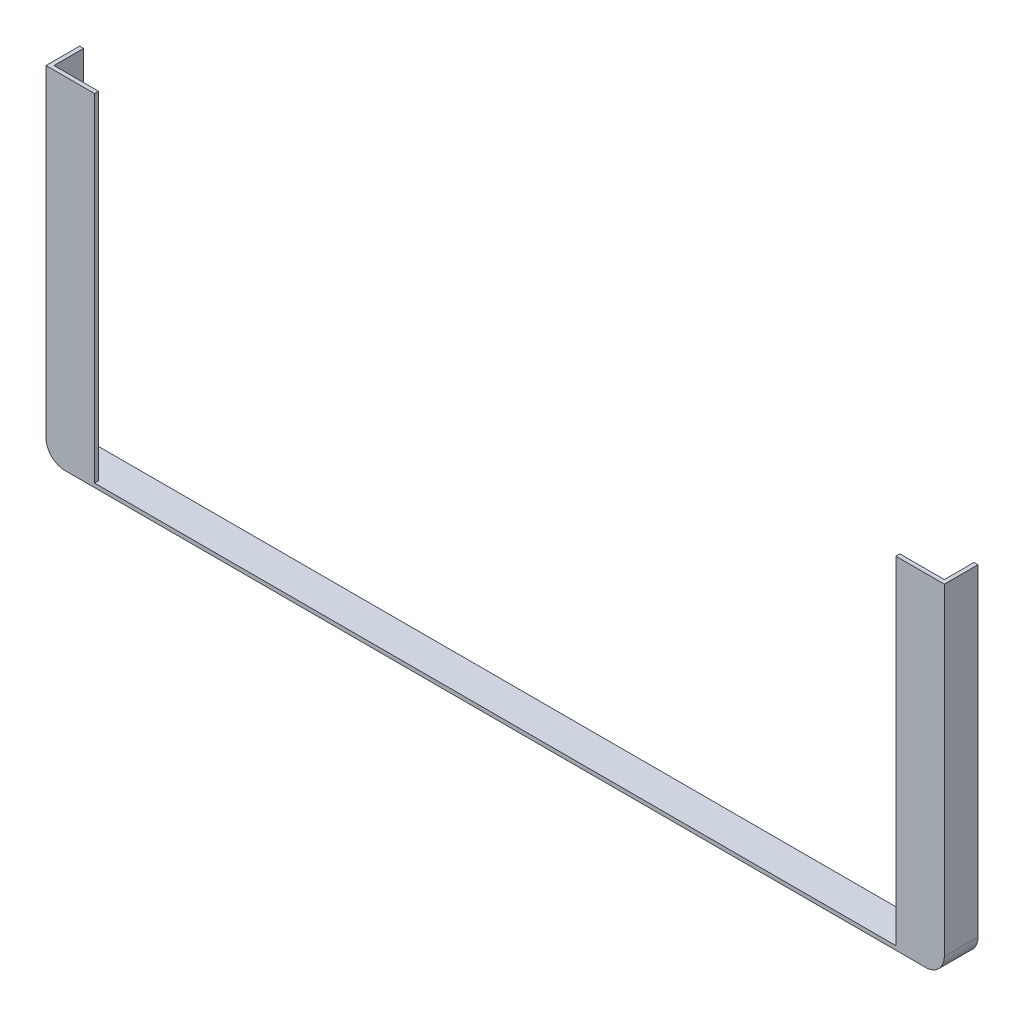
SolidWorks part; units mm, degrees
material "Plain Carbon Steel"
ref_plane "Front Plane" through (0, 0, 0) normal (0, 0, 1) x (1, 0, 0)
ref_plane "Top Plane" through (0, 0, 0) normal (0, 1, 0) x (1, 0, 0)
ref_plane "Right Plane" through (0, 0, 0) normal (1, 0, 0) x (0, 0, -1)
sketch "Sketch2" plane through (0, 0, 0) normal (0, 0, 1) x (1, 0, 0)
  line L1 (-381, 12.7) -> (-381, 288.6837)
  line L4 (381, 12.7) -> (381, 288.6837)
  line L5 (-368.3, 0) -> (368.3, 0)
  line L6 (384.4163, 12.7) -> (384.4163, 288.6837)
  line L7 (-368.3, -3.4163) -> (368.3, -3.4163)
  line L8 (-384.4163, 12.7) -> (-384.4163, 288.6837)
  line L9 (381, 288.6837) -> (384.4163, 288.6837)
  line L10 (-384.4163, 288.6837) -> (-381, 288.6837)
  arc A2 (368.3, 0) -> (381, 12.7) centre (368.3, 12.7) ccw
  arc A3 (-381, 12.7) -> (-368.3, 0) centre (-368.3, 12.7) ccw
  arc A4 (368.3, -3.4163) -> (384.4163, 12.7) centre (368.3, 12.7) ccw
  arc A5 (-384.4163, 12.7) -> (-368.3, -3.4163) centre (-368.3, 12.7) ccw
  point P16 (0, 0)
  dimension "D2" = 12.7
  dimension "D3" = 292.1
  dimension "D4" = 768.8326
  dimension "D1" = 3.4163
extrude "Side" add sketch "Sketch2" against normal blind 25.4
sketch "Sketch3" plane through (0, 0, 0) normal (0, 0, 1) x (1, 0, 0)
  line L0 (-368.3, -3.4163) -> (368.3, -3.4163) construction
  line L1 (-384.4163, 288.6837) -> (-384.4163, 12.7) construction
  line L2 (-368.3, -3.4163) -> (368.3, -3.4163)
  line L3 (-384.4163, 288.6837) -> (-384.4163, 12.7)
  line L4 (384.4163, 12.7) -> (384.4163, 288.6837) construction
  line L5 (384.4163, 12.7) -> (384.4163, 288.6837)
  line L6 (384.4163, 288.6837) -> (-384.4163, 288.6837)
  arc A0 (-384.4163, 12.7) -> (-368.3, -3.4163) centre (-368.3, 12.7) ccw construction
  arc A1 (-384.4163, 12.7) -> (-368.3, -3.4163) centre (-368.3, 12.7) ccw
  arc A2 (368.3, -3.4163) -> (384.4163, 12.7) centre (368.3, 12.7) ccw construction
  arc A3 (368.3, -3.4163) -> (384.4163, 12.7) centre (368.3, 12.7) ccw
extrude "Panel" add sketch "Sketch3" along normal blind 3.4163
sketch "Sketch4" plane through (0, 0, 0) normal (0, 0, -1) x (-1, 0, 0)
  line L0 (-368.3, 0) -> (368.3, 0) construction
  line L1 (-342.9, 0) -> (342.9, 0)
  line L2 (-342.9, 0) -> (-342.9, 288.6837)
  line L3 (-342.9, 288.6837) -> (342.9, 288.6837)
  line L4 (342.9, 0) -> (342.9, 288.6837)
  line L5 (-381, 288.6837) -> (381, 288.6837) construction
  line L6 (-381, 288.6837) -> (-381, 12.7) construction
  line L7 (381, 12.7) -> (381, 288.6837) construction
  dimension "D1" = 38.1
  dimension "D2" = 38.1
extrude "Back Cut" cut sketch "Sketch4" against normal up to next
